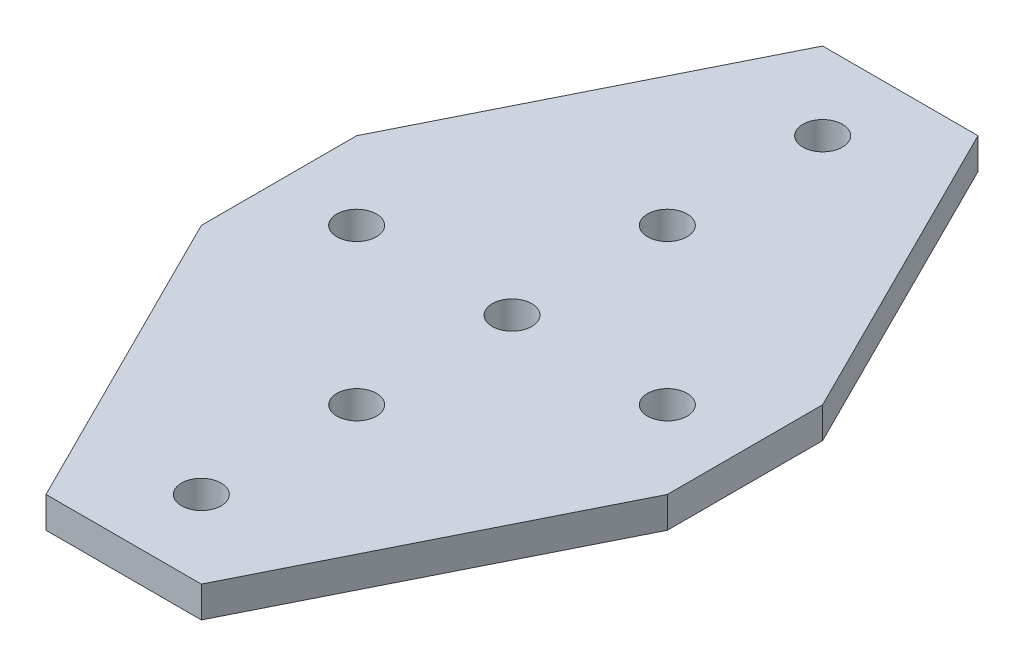
SolidWorks part; units mm, degrees
material "6061-T6 (SS)"
ref_plane "Front Plane" through (0, 0, 0) normal (0, 0, 1) x (1, 0, 0)
ref_plane "Top Plane" through (0, 0, 0) normal (0, 1, 0) x (1, 0, 0)
ref_plane "Right Plane" through (0, 0, 0) normal (1, 0, 0) x (0, 0, -1)
sketch "Sketch1" plane through (0, 0, 0) normal (0, 1, 0) x (1, 0, 0)
  line L0 (-30, 0) -> (0, 0) construction
  line L1 (30, -10) -> (10, -50)
  line L2 (-10, 50) -> (10, 50)
  line L3 (0, 0) -> (0, 50) construction
  line L4 (-30, -10) -> (-30, 10)
  line L5 (-10, -50) -> (10, -50)
  line L6 (-30, -10) -> (-10, -50)
  line L7 (-30, 10) -> (-10, 50)
  line L8 (30, -10) -> (30, 10)
  line L10 (30, 10) -> (10, 50)
  circle A0 centre (0, 20) radius 2.55
  circle A1 centre (0, 40) radius 2.55
  circle A2 centre (0, 0) radius 2.55
  circle A3 centre (0, -20) radius 2.55
  circle A4 centre (0, -40) radius 2.55
  circle A5 centre (-20, 0) radius 2.55
  circle A6 centre (20, 0) radius 2.55
  dimension "D3" = 100
  dimension "D2" = 5.1
  dimension "D1" = 20
  dimension "D4" = 20
  dimension "D5" = 60
  dimension "D7" = 20
  dimension "D11" = 20
  dimension "D6" = 20
extrude "Boss-Extrude1" add sketch "Sketch1" along normal blind 4
